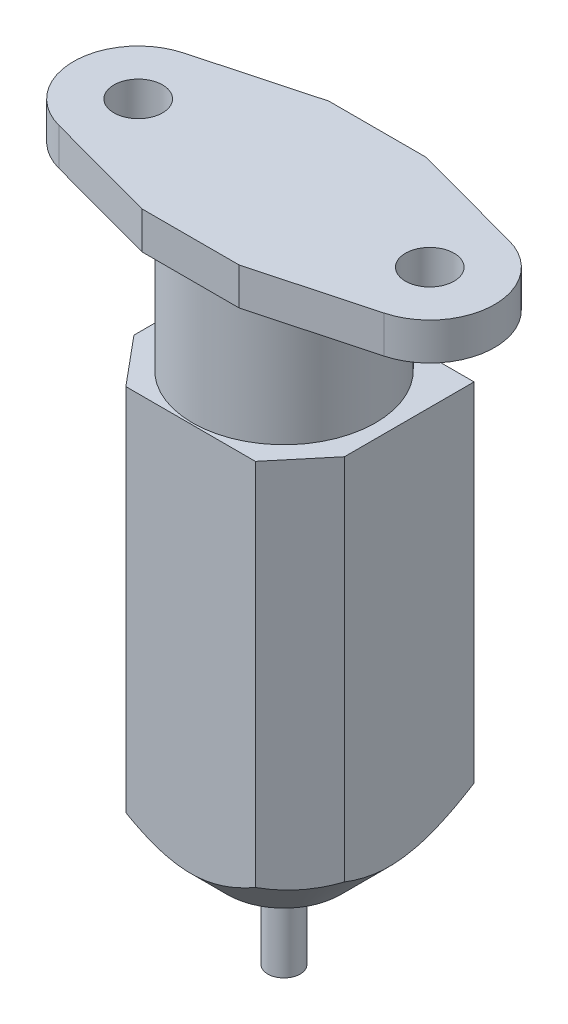
SolidWorks part; units mm, degrees
ref_plane "Front Plane" through (0, 0, 0) normal (0, 0, 1) x (1, 0, 0)
ref_plane "Top Plane" through (0, 0, 0) normal (0, 1, 0) x (1, 0, 0)
ref_plane "Right Plane" through (0, 0, 0) normal (1, 0, 0) x (0, 0, -1)
sketch "Sketch1" plane through (0, 0, 0) normal (0, 1, 0) x (1, 0, 0)
  line L0 (0, 0) -> (0, 5.765) construction
  line L1 (0, 0) -> (9, 0) construction
  line L2 (-3, 5.765) -> (3, 5.765)
  line L3 (3, 5.765) -> (10.0436, 3.8615)
  line L4 (-3, -5.765) -> (3, -5.765)
  line L5 (3, -5.765) -> (10.0436, -3.8615)
  line L6 (-3, 5.765) -> (-10.0436, 3.8615)
  line L7 (-3, -5.765) -> (-10.0436, -3.8615)
  circle A0 centre (9, 0) radius 1.5
  arc A1 (10.0436, 3.8615) -> (10.0436, -3.8615) centre (9, 0) cw
  arc A2 (-10.0436, 3.8615) -> (-10.0436, -3.8615) centre (-9, 0) ccw
  circle A3 centre (-9, 0) radius 1.5
  point P19 (0, -5.765)
  dimension "D3" = 3
  dimension "D6" = 4
  dimension "D1" = 11.53
  dimension "D4" = 9
  dimension "D5" = 6
extrude "Boss-Extrude1" add sketch "Sketch1" against normal blind 2.3
sketch "Sketch2" plane through (0, -2.3, 0) normal (0, -1, 0) x (1, 0, 0)
  circle A0 centre (0, 0) radius 5.65
  dimension "D1" = 11.3
extrude "Boss-Extrude2" add sketch "Sketch2" along normal blind 7.7
sketch "Sketch3" plane through (0, -10, 0) normal (0, -1, 0) x (1, 0, 0)
  line L0 (-4, 5.765) -> (4, 5.765)
  line L1 (-3, 5.765) -> (3, 5.765) construction
  line L2 (4, 5.765) -> (6.5, 2.765)
  line L3 (6.5, 2.765) -> (6.5, -5.235)
  line L4 (6.5, -5.235) -> (-6.5, -5.235)
  line L5 (0, 5.765) -> (0, 0) construction
  line L6 (0, 0) -> (0, -5.235) construction
  line L7 (-6.5, 2.765) -> (-6.5, -5.235)
  line L8 (-4, 5.765) -> (-6.5, 2.765)
  dimension "D1" = 13
  dimension "D2" = 11
  dimension "D3" = 8
  dimension "D4" = 3
extrude "Boss-Extrude3" add sketch "Sketch3" along normal blind 26.3
sketch "Sketch4" plane through (0, 0, 0) normal (0, 0, 1) x (1, 0, 0)
  line L0 (0, -36.3) -> (0, 0) construction
  line L1 (4, -36.3) -> (-4, -36.3) construction
  line L2 (3.5, -36.3) -> (10, -29.8)
  line L3 (10, -29.8) -> (10, -36.3)
  line L4 (10, -36.3) -> (3.5, -36.3)
  dimension "D1" = 7
  dimension "D2" = 45
  dimension "D3" = 20
revolve "Cut-Revolve1" cut sketch "Sketch4" angle 360 about L0
sketch "Sketch5" plane through (0, -36.3, 0) normal (0, -1, 0) x (1, 0, 0)
  circle A0 centre (0, 0) radius 1
  dimension "D1" = 2
extrude "Boss-Extrude4" add sketch "Sketch5" along normal blind 5.5
